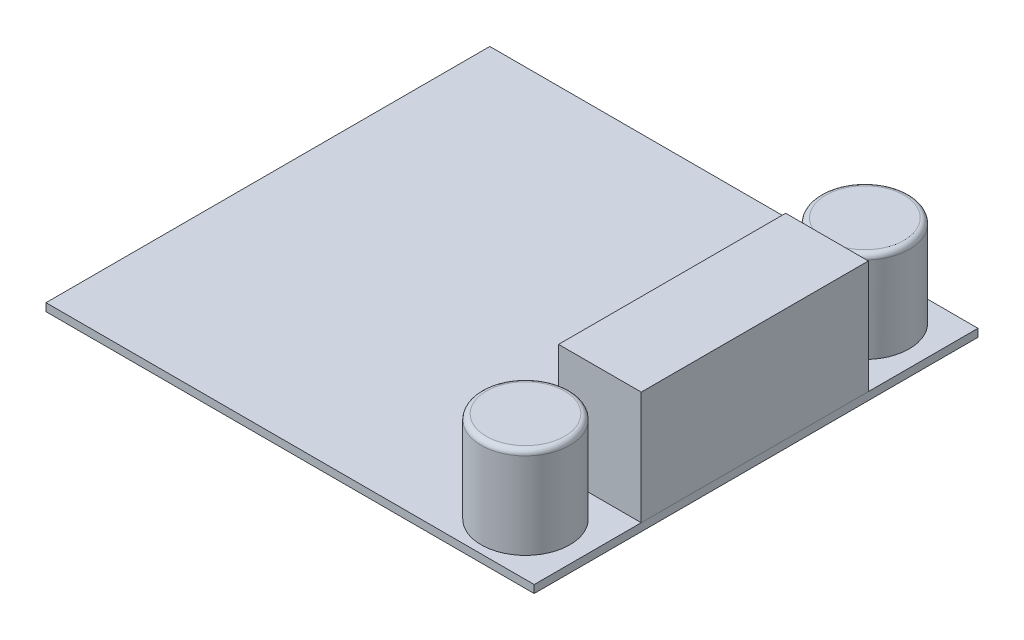
SolidWorks part; units mm, degrees
ref_plane "Ebene vorne" through (0, 0, 0) normal (0, 0, 1) x (1, 0, 0)
ref_plane "Ebene oben" through (0, 0, 0) normal (0, 1, 0) x (1, 0, 0)
ref_plane "Ebene rechts" through (0, 0, 0) normal (1, 0, 0) x (0, 0, -1)
sketch "Skizze1" plane through (0, 0, 0) normal (0, 1, 0) x (1, 0, 0)
  line L1 (-28.05, -25.5) -> (28.05, -25.5)
  line L2 (-28.05, -25.5) -> (-28.05, 25.5)
  line L3 (-28.05, 25.5) -> (28.05, 25.5)
  line L4 (28.05, -25.5) -> (28.05, 25.5)
  line L5 (-28.05, -25.5) -> (28.05, 25.5) construction
  line L6 (-28.05, 25.5) -> (28.05, -25.5) construction
  point P0 (0, 0)
  dimension "D1" = 56.1
  dimension "D2" = 51
extrude "Aufsatz-Linear austragen1" add sketch "Skizze1" along normal blind 0.9
sketch "Skizze2" plane through (0, 0.9, 0) normal (0, 1, 0) x (1, 0, 0)
  line L0 (28.05, -25.5) -> (28.05, 25.5) construction
  line L1 (18.55, 12.9) -> (28.05, 12.9)
  line L2 (18.55, 12.9) -> (18.55, -13.2)
  line L3 (18.55, -13.2) -> (28.05, -13.2)
  line L4 (28.05, 12.9) -> (28.05, -13.2)
  line L5 (-28.05, -25.5) -> (28.05, -25.5) construction
  dimension "D1" = 9.5
  dimension "D2" = 26.1
  dimension "D3" = 12.3
extrude "Aufsatz-Linear austragen2" add sketch "Skizze2" along normal blind 13 separate body
sketch "Skizze3" plane through (0, 0.9, 0) normal (0, 1, 0) x (1, 0, 0)
  line L0 (-52.484, 0) -> (52.2206, 0) construction
  line L1 (28.05, -25.5) -> (28.05, 25.5) construction
  circle A0 centre (21.05, 19.5) radius 5.1
  circle A1 centre (21.05, -19.5) radius 5.1
  dimension "D1" = 10.2
  dimension "D2" = 39
  dimension "D3" = 7
extrude "Aufsatz-Linear austragen3" add sketch "Skizze3" along normal blind 10.5
fillet "Verrundung1" radius 0.6 2 edges at (21.05, 11.4, -14.4) (21.05, 11.4, 14.4)
